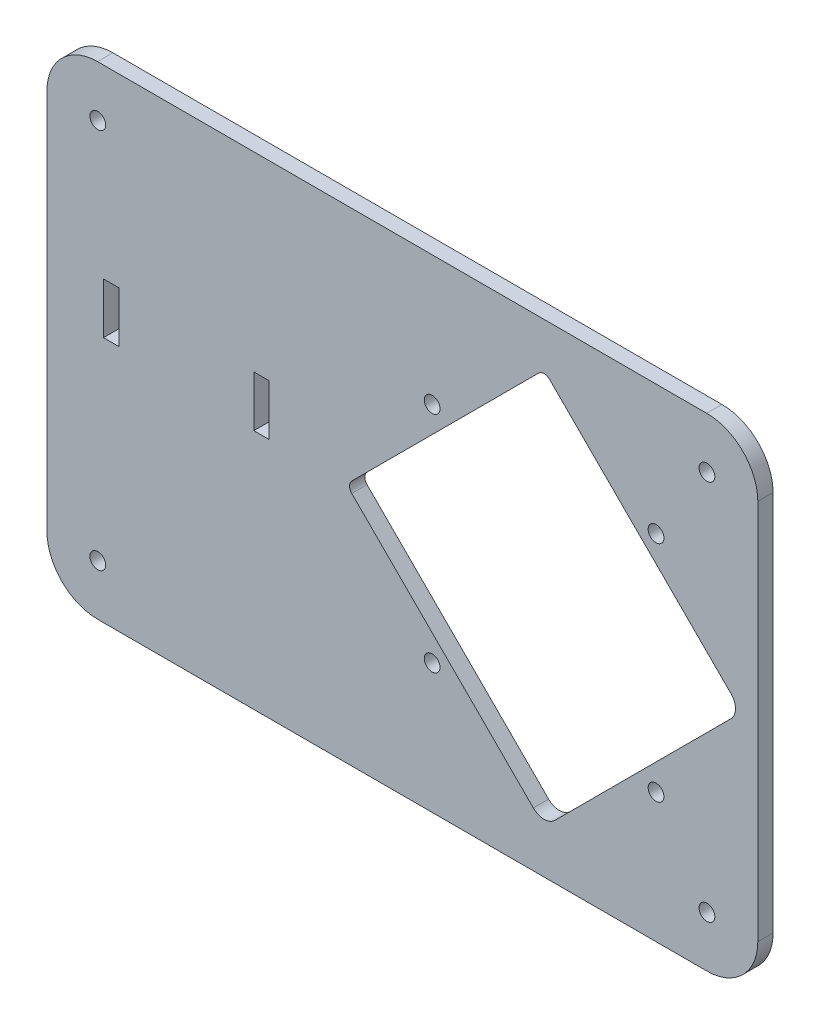
SolidWorks part; units mm, degrees
ref_plane "Front Plane" through (0, 0, 0) normal (0, 0, 1) x (1, 0, 0)
ref_plane "Top Plane" through (0, 0, 0) normal (0, 1, 0) x (1, 0, 0)
ref_plane "Right Plane" through (0, 0, 0) normal (1, 0, 0) x (0, 0, -1)
sketch "Model" plane through (0, 0, 0) normal (0, 0, 1) x (1, 0, 0)
  line L0 (15.6948, -8.8473) -> (135.3948, -8.8473)
  line L1 (101.2735, 1.8663) -> (65.6001, 37.5397)
  line L2 (105.5161, 1.8663) -> (140.1289, 36.4791)
  line L3 (65.6001, 39.6611) -> (102.3341, 76.3951)
  line L4 (140.1289, 40.7217) -> (104.4554, 76.3951)
  line L5 (15.6524, 86.0577) -> (135.3525, 86.0577)
  line L6 (145.3948, 76.1) -> (145.3948, 1.1527)
  line L7 (5.6948, 76.1001) -> (5.6948, 1.1527)
  line L9 (16.8158, 49.6611) -> (19.8158, 49.6611)
  line L10 (16.8158, 49.6611) -> (16.8158, 39.6611)
  line L11 (16.8158, 39.6611) -> (19.8158, 39.6611)
  line L12 (19.8158, 49.6611) -> (19.8158, 39.6611)
  line L13 (46.3486, 48.6004) -> (49.3486, 48.6004)
  line L14 (46.3486, 48.6004) -> (46.3486, 38.6004)
  line L15 (46.3486, 38.6004) -> (49.3486, 38.6004)
  line L16 (49.3486, 48.6004) -> (49.3486, 38.6004)
  arc A0 (101.2735, 1.8663) -> (105.5161, 1.8663) centre (103.3948, 3.9876) ccw
  arc A1 (140.1289, 36.4791) -> (140.1289, 40.7217) centre (138.0075, 38.6004) ccw
  arc A2 (104.4554, 76.3951) -> (102.3341, 76.3951) centre (103.3948, 75.3345) ccw
  arc A3 (65.6001, 39.6611) -> (65.6001, 37.5397) centre (66.6608, 38.6004) ccw
  arc A4 (15.6524, 86.0577) -> (5.6948, 76.1001) centre (15.6948, 76.0577) ccw
  circle A9 centre (81.3949, 16.6) radius 1.55
  circle A10 centre (81.3947, 60.6001) radius 1.55
  circle A11 centre (125.3948, 16.6) radius 1.55
  circle A12 centre (125.3949, 60.6) radius 1.55
  arc A13 (145.3948, 76.1) -> (135.3525, 86.0577) centre (135.3948, 76.0577) ccw
  arc A14 (135.3948, -8.8473) -> (145.3948, 1.1527) centre (135.3948, 1.1527) ccw
  circle A15 centre (135.3948, 76.0577) radius 1.55
  circle A16 centre (135.3948, 1.1527) radius 1.55
  circle A17 centre (15.6948, 76.0577) radius 1.55
  circle A18 centre (15.6948, 1.1527) radius 1.55
  arc A19 (5.6948, 1.1527) -> (15.6948, -8.8473) centre (15.6948, 1.1527) ccw
  dimension "D1" = 10
  dimension "D2" = 10
  dimension "D3" = 10
  dimension "D4" = 10
  dimension "D5" = 10
  dimension "D6" = 10
  dimension "D7" = 10
  dimension "D8" = 10
  dimension "D9" = 139.7
  dimension "D10" = 119.7
  dimension "D11" = 10
  dimension "D12" = 10
  dimension "D13" = 3
  dimension "D14" = 3
extrude "Boss-Extrude1" add sketch "Model" along normal blind 3
